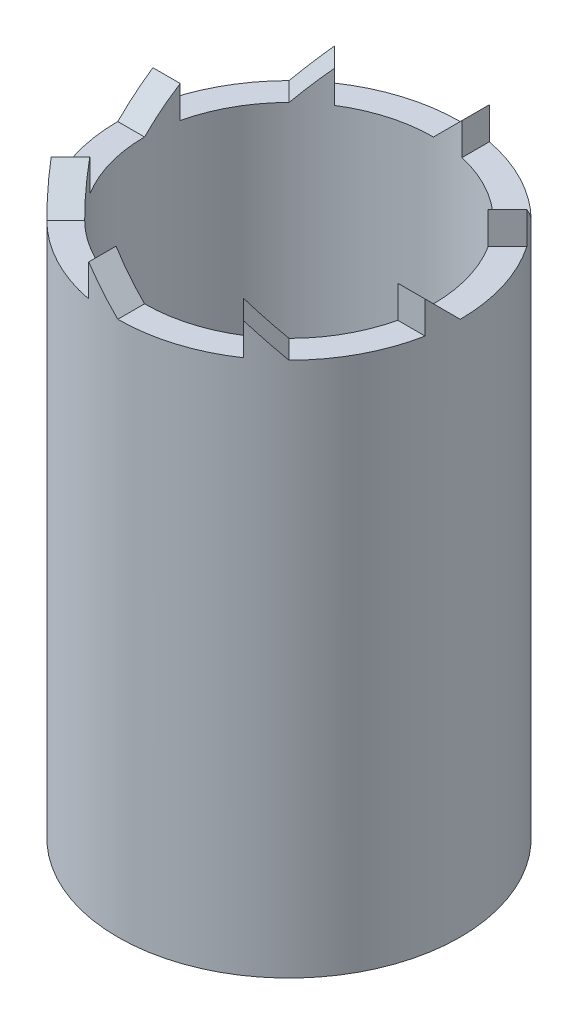
SolidWorks part; units mm, degrees
ref_plane "Front" through (0, 0, 0) normal (0, 0, 1) x (1, 0, 0)
ref_plane "Top" through (0, 0, 0) normal (0, 1, 0) x (1, 0, 0)
ref_plane "Right" through (0, 0, 0) normal (1, 0, 0) x (0, 0, -1)
sketch "Sketch1" plane through (0, 0, 0) normal (0, 1, 0) x (1, 0, 0)
  circle A0 centre (0, 0) radius 6.75
  circle A1 centre (0, 0) radius 8.25
  dimension "D1" = 13.5
  dimension "D2" = 16.5
extrude "Boss-Extrude1" add sketch "Sketch1" along normal blind 25
sketch "Sketch2" plane through (0, 25, 0) normal (0, 1, 0) x (1, 0, 0)
  line L0 (0, -8.25) -> (0, 8.25) construction
  line L1 (-8.25, 0) -> (8.25, 0) construction
  line L3 (0, 8.25) -> (1.5, 8.25)
  line L4 (0, 8.25) -> (0, 6.5)
  line L5 (0, 6.5) -> (1.5, 6.5)
  line L6 (1.5, 8.25) -> (1.5, 6.5)
  line L7 (8.25, 0) -> (6.5, 0)
  line L8 (8.25, 0) -> (8.25, -1.5)
  line L9 (8.25, -1.5) -> (6.5, -1.5)
  line L10 (6.5, 0) -> (6.5, -1.5)
  line L11 (0, -8.25) -> (-1.5, -8.25)
  line L12 (0, -8.25) -> (0, -6.5)
  line L13 (0, -6.5) -> (-1.5, -6.5)
  line L14 (-1.5, -8.25) -> (-1.5, -6.5)
  line L15 (-8.25, 0) -> (-6.5, 0)
  line L16 (-8.25, 0) -> (-8.25, 1.4996)
  line L17 (-8.25, 1.4996) -> (-6.5, 1.4996)
  line L18 (-6.5, 0) -> (-6.5, 1.4996)
  line L19 (-5.8336, 5.8336) -> (5.8336, -5.8336) construction
  line L21 (-5.8336, -5.8336) -> (5.8336, 5.8336) construction
  line L32 (-5.8336, 5.8336) -> (-4.773, 6.8943)
  line L33 (-4.773, 6.8943) -> (-3.5355, 5.6569)
  line L34 (-3.5355, 5.6569) -> (-4.5962, 4.5962)
  line L35 (-4.5962, 4.5962) -> (-5.8336, 5.8336)
  line L36 (5.8336, 5.8336) -> (6.8943, 4.773)
  line L37 (6.8943, 4.773) -> (5.6569, 3.5355)
  line L38 (5.6569, 3.5355) -> (4.5962, 4.5962)
  line L39 (4.5962, 4.5962) -> (5.8336, 5.8336)
  line L40 (5.8336, -5.8336) -> (4.773, -6.8943)
  line L41 (4.773, -6.8943) -> (3.5355, -5.6569)
  line L42 (3.5355, -5.6569) -> (4.5962, -4.5962)
  line L43 (4.5962, -4.5962) -> (5.8336, -5.8336)
  line L44 (-5.8336, -5.8336) -> (-6.8943, -4.773)
  line L45 (-6.8943, -4.773) -> (-5.6569, -3.5355)
  line L46 (-5.6569, -3.5355) -> (-4.5962, -4.5962)
  line L47 (-4.5962, -4.5962) -> (-5.8336, -5.8336)
  circle A0 centre (0, 0) radius 8.25 construction
  dimension "D9" = 45
  dimension "D1" = 1.5
  dimension "D2" = 1.75
  dimension "D3" = 1.5
  dimension "D4" = 1.75
  dimension "D5" = 1.5
  dimension "D6" = 1.75
  dimension "D7" = 1.4996
  dimension "D8" = 1.75
  dimension "D10" = 45
  dimension "D11" = 1.5
  dimension "D12" = 1.75
  dimension "D13" = 1.5
extrude "Boss-Extrude2" add sketch "Sketch2" along normal blind 1.5
sketch "Sketch5" plane through (0, 0, 8.25) normal (0, 0, 1) x (1, 0, 0)
  line L3 (-1.5, 26.5) -> (0, 25)
  line L7 (-1.5, 26.5) -> (0, 26.5)
  line L8 (0, 26.5) -> (0, 25)
extrude "Cut-Extrude1" cut sketch "Sketch5" against normal blind 2.5
sketch "Sketch6" plane through (-8.25, 0, 0) normal (-1, 0, 0) x (0, 0, 1)
  line L2 (0, 26.5) -> (-1.4996, 26.5)
  line L4 (-1.4996, 26.5) -> (0, 25)
  line L5 (0, 25) -> (0, 26.5)
extrude "Cut-Extrude2" cut sketch "Sketch6" against normal blind 2.5
sketch "Sketch7" plane through (0, 0, -8.25) normal (0, 0, -1) x (-1, 0, 0)
  line L1 (-1.5, 26.5) -> (0, 26.5)
  line L3 (-1.5, 26.5) -> (0, 25)
  line L4 (0, 25) -> (0, 26.5)
extrude "Cut-Extrude3" cut sketch "Sketch7" against normal blind 2.5
sketch "Sketch8" plane through (8.25, 0, 0) normal (1, 0, 0) x (0, 0, -1)
  line L1 (0, 26.5) -> (-1.5, 26.5)
  line L3 (0, 26.5) -> (0, 25)
  line L4 (0, 25) -> (-1.5, 26.5)
extrude "Cut-Extrude4" cut sketch "Sketch8" against normal blind 2.5
sketch "Sketch9" plane through (0, 25, 0) normal (0, 1, 0) x (1, 0, 0)
  circle A0 centre (0, 0) radius 6.625
  dimension "D1" = 13.25
extrude "Cut-Extrude7" cut sketch "Sketch9" along normal blind 2.5
sketch "Sketch11" plane through (-5.8336, 0, 5.8336) normal (-0.7071, 0, 0.7071) x (0.7071, 0, 0.7071)
  line L0 (0, 25) -> (-1.5, 26.5)
  line L3 (-1.5, 26.5) -> (0, 26.5)
  line L4 (0, 26.5) -> (0, 25)
extrude "Cut-Extrude10" cut sketch "Sketch11" against normal through all
sketch "Sketch12" plane through (-5.8336, 0, -5.8336) normal (-0.7071, 0, -0.7071) x (-0.7071, 0, 0.7071)
  line L0 (0, 25) -> (-1.5, 26.5)
  line L1 (-1.5, 26.5) -> (0, 26.5)
  line L2 (0, 26.5) -> (0, 25)
extrude "Cut-Extrude11" cut sketch "Sketch12" against normal through all
sketch "Sketch13" plane through (5.8336, 0, -5.8336) normal (0.7071, 0, -0.7071) x (-0.7071, 0, -0.7071)
  line L0 (0, 25) -> (-1.5, 26.5)
  line L1 (-1.5, 26.5) -> (0, 26.5)
  line L2 (0, 26.5) -> (0, 25)
extrude "Cut-Extrude12" cut sketch "Sketch13" against normal through all
sketch "Sketch14" plane through (5.8336, 0, 5.8336) normal (0.7071, 0, 0.7071) x (0.7071, 0, -0.7071)
  line L0 (0, 25) -> (-1.5, 26.5)
  line L1 (-1.5, 26.5) -> (0, 26.5)
  line L2 (0, 26.5) -> (0, 25)
extrude "Cut-Extrude13" cut sketch "Sketch14" against normal through all
sketch "Sketch15" plane through (0, 0, 0) normal (0, -1, 0) x (1, 0, 0)
  circle A0 centre (0, 0) radius 8
  circle A1 centre (0, 0) radius 10.3323
extrude "Cut-Extrude14" cut sketch "Sketch15" against normal blind 35
sketch "Sketch16" plane through (0, 0, 0) normal (0, 1, 0) x (1, 0, 0)
  circle A0 centre (0, 0) radius 6.75
extrude "Cut-Extrude15" cut sketch "Sketch16" along normal blind 40
